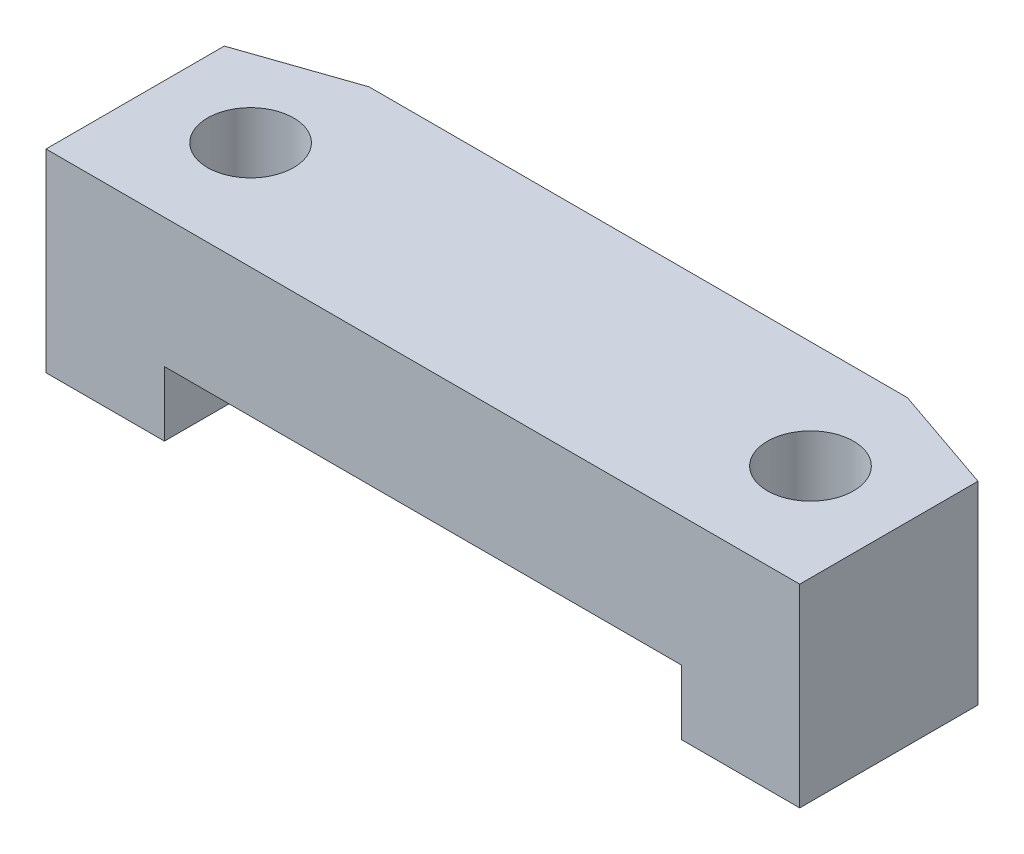
SolidWorks part; units mm, degrees
material "2024-T3"
ref_plane "Спереди" through (0, 0, 0) normal (0, 0, 1) x (1, 0, 0)
ref_plane "Сверху" through (0, 0, 0) normal (0, 1, 0) x (1, 0, 0)
ref_plane "Справа" through (0, 0, 0) normal (1, 0, 0) x (0, 0, -1)
sketch "Эскиз1" plane through (0, 0, 0) normal (0, 0, 1) x (1, 0, 0)
  line L1 (0, 0) -> (17.5, 0)
  line L2 (0, 0) -> (0, 4.5)
  line L3 (0, 4.5) -> (17.5, 4.5)
  line L4 (17.5, 0) -> (17.5, 4.5)
  dimension "D1" = 17.5
  dimension "D2" = 4.5
extrude "Бобышка-Вытянуть1" add sketch "Эскиз1" along normal blind 5
sketch "Эскиз2" plane through (0, 4.5, 0) normal (0, 1, 0) x (1, 0, 0)
  line L2 (2.25, -2.5) -> (0, -2.5) construction
  line L5 (15.25, -2.5) -> (17.5, -2.5) construction
  line L8 (0, -5) -> (0, 0) construction
  line L9 (17.5, -5) -> (17.5, 0) construction
  circle A0 centre (2.25, -2.5) radius 1
  circle A1 centre (15.25, -2.5) radius 1
  dimension "D1" = 13
  dimension "D4" = 2
extrude "Вырез-Вытянуть1" cut sketch "Эскиз2" against normal through all
sketch "Эскиз3" plane through (0, 0, 5) normal (0, 0, 1) x (1, 0, 0)
  line L0 (2.75, 0) -> (2.75, 1.5)
  line L1 (0, 0) -> (17.5, 0) construction
  line L2 (2.75, 1.5) -> (14.75, 1.5)
  line L3 (14.75, 1.5) -> (14.75, 0)
  line L4 (0, 0) -> (2.75, 0) construction
  line L5 (14.75, 0) -> (17.5, 0) construction
  line M4 (0, 0) -> (17.5, 0)
  dimension "D1" = 12
  dimension "D2" = 1.5
extrude "Вырез-Вытянуть3" cut sketch "Эскиз3" against normal through all contours L3 L2 L0 M4
chamfer "Фаска1" [suppressed] distance 1 angle 70
sketch "Эскиз4" plane through (0, 4.5, 0) normal (0, 1, 0) x (1, 0, 0)
  circle A0 centre (2.25, -2.5) radius 1.8
  circle A1 centre (15.25, -2.5) radius 1.8
  dimension "D1" = 3.6
extrude "Вырез-Вытянуть4" [suppressed] cut sketch "Эскиз4" against normal offset from surface (2 mm away) 1
chamfer "Фаска2" distance 2.5 angle 19 2 edges at (0, 2.25, 0) (17.5, 2.25, 0)
